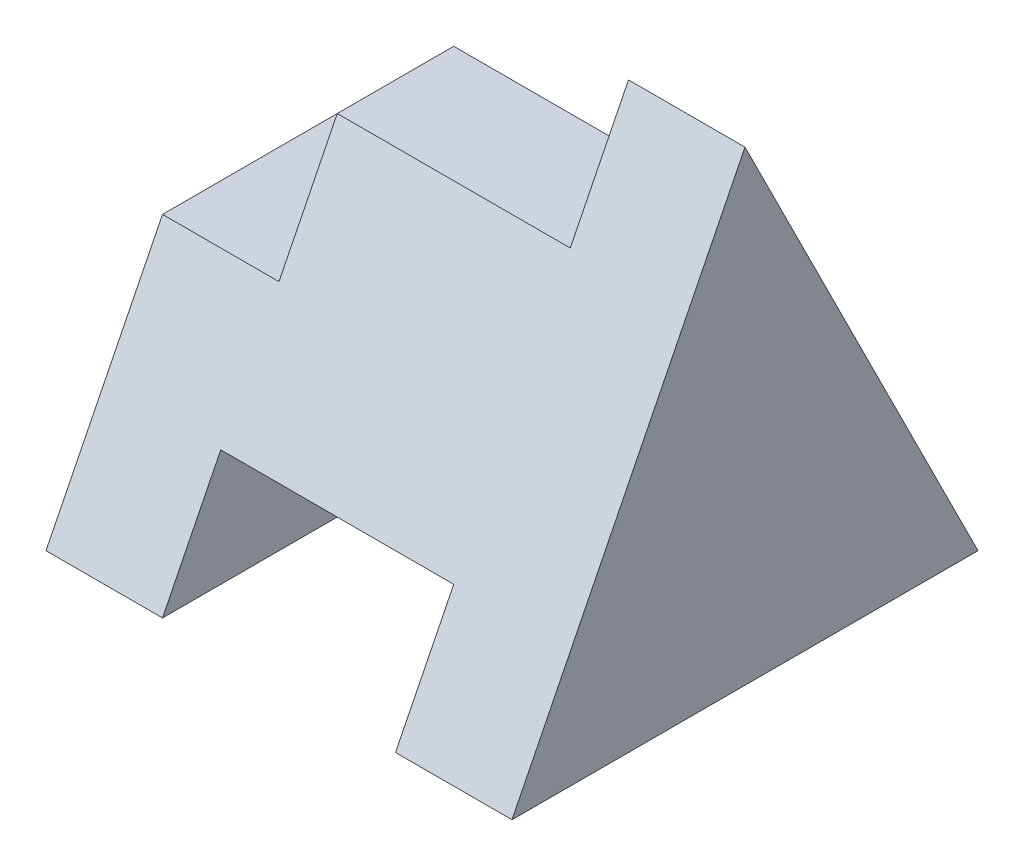
SolidWorks part; units mm, degrees
ref_plane "Front" through (0, 0, 0) normal (0, 0, 1) x (1, 0, 0)
ref_plane "Top" through (0, 0, 0) normal (0, 1, 0) x (1, 0, 0)
ref_plane "Right" through (0, 0, 0) normal (1, 0, 0) x (0, 0, -1)
sketch "Sketch1" plane through (0, 0, 0) normal (0, 0, 1) x (1, 0, 0)
  line L0 (0, 0) -> (0, 2)
  line L1 (0, 2) -> (1, 2)
  line L2 (1, 2) -> (1, 3)
  line L3 (1, 3) -> (3, 3)
  line L4 (3, 3) -> (3, 4)
  line L5 (3, 4) -> (4, 4)
  line L6 (4, 4) -> (4, 0)
  line L7 (4, 0) -> (3, 0)
  line L8 (3, 0) -> (3, 1)
  line L9 (3, 1) -> (1, 1)
  line L10 (1, 1) -> (1, 0)
  line L11 (1, 0) -> (0, 0)
  dimension "D1" = 4
  dimension "D2" = 1
  dimension "D3" = 1
  dimension "D4" = 1
  dimension "D5" = 1
  dimension "D6" = 2
  dimension "D7" = 1
  dimension "D8" = 1
  dimension "D9" = 2
extrude "Boss-Extrude1" add sketch "Sketch1" along normal blind 4
sketch "Sketch3" plane through (0, 0, 0) normal (-1, 0, 0) x (0, 0, 1)
  line L0 (4, 0) -> (2, 4)
  line L3 (2, 4) -> (0, 0)
  line L4 (0, 0) -> (0, 4)
  line L5 (0, 4) -> (4, 4)
  line L6 (4, 4) -> (4, 0)
  line M4 (0, 2) -> (0, 0)
  line M6 (4, 0) -> (4, 2)
  line M7 (4, 2) -> (0, 2)
extrude "Cut-Extrude2" cut sketch "Sketch3" against normal blind 10 contours L5 L4 L3 M7 | L3 M7 M4 | L6 L5 L0 M7 | L0 M6 M7
